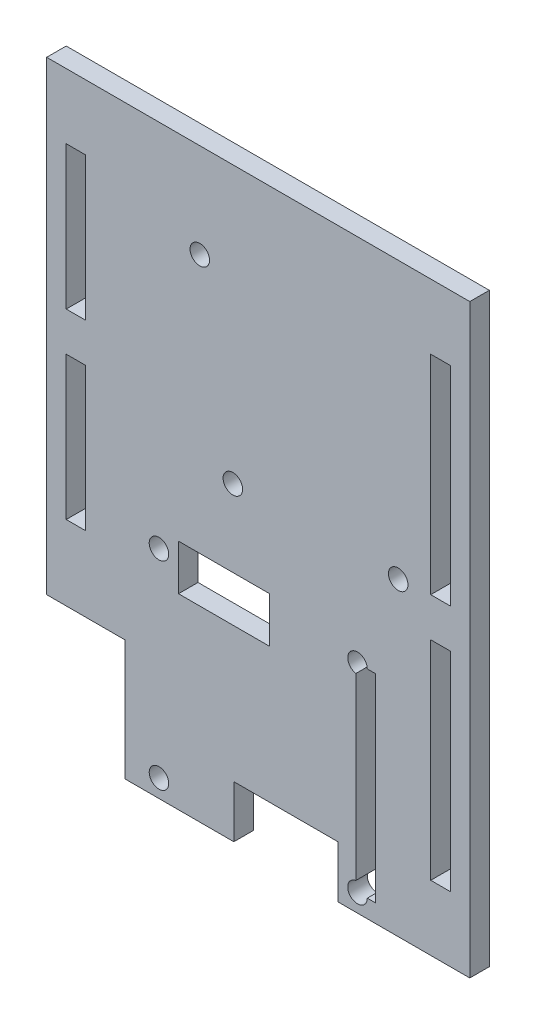
SolidWorks part; units mm, degrees
material "Custom Plastic"
ref_plane "Front Plane" through (0, 0, 0) normal (0, 0, 1) x (1, 0, 0)
ref_plane "Top Plane" through (0, 0, 0) normal (0, 1, 0) x (1, 0, 0)
ref_plane "Right Plane" through (0, 0, 0) normal (1, 0, 0) x (0, 0, -1)
sketch "Sketch1" plane through (0, 0, 0) normal (0, 0, 1) x (1, 0, 0)
  line L1 (-32.5, 45) -> (32.5, 45)
  line L2 (-32.5, 45) -> (-32.5, -45)
  line L3 (-32.5, -45) -> (32.5, -45)
  line L4 (32.5, 45) -> (32.5, -45)
  line L5 (-32.5, 45) -> (32.5, -45) construction
  line L6 (-32.5, -45) -> (32.5, 45) construction
  point P0 (0, 0)
  dimension "D1" = 65
  dimension "D2" = 90
extrude "Boss-Extrude1" add sketch "Sketch1" against normal blind 3
sketch "Sketch3" plane through (0, 0, 0) normal (0, 0, 1) x (1, 0, 0)
  line L0 (32.5, -45) -> (32.5, 45) construction
  line L3 (21.5, 2.56) -> (-3.9, 2.56) construction
  line L4 (32.5, 45) -> (-32.5, 45) construction
  circle A0 centre (-8.98, 30.5) radius 1.5
  circle A1 centre (-3.9, 2.56) radius 1.5
  circle A2 centre (21.5, 2.56) radius 1.5
  dimension "D5" = 3
  dimension "D6" = 3
  dimension "D7" = 3
  dimension "D1" = 27.94
  dimension "D2" = 5.08
  dimension "D3" = 25.4
  dimension "D4" = 14.5
  dimension "D8" = 11
extrude "Cut-Extrude2" cut sketch "Sketch3" against normal blind 3
sketch "Sketch4" plane through (0, 0, 0) normal (0, 0, 1) x (1, 0, 0)
  line L0 (-15.25, -11.75) -> (-15.25, -42.25) construction
  line L1 (-15.25, -42.25) -> (15.25, -42.25) construction
  line L2 (15.25, -42.25) -> (15.25, -11.75) construction
  circle A0 centre (-15.25, -42.25) radius 1.5
  circle A1 centre (-15.25, -11.75) radius 1.5
  circle A2 centre (15.25, -42.25) radius 1.5
  circle A3 centre (15.25, -11.75) radius 1.5
  dimension "D3" = 3
  dimension "D1" = 30.5
  dimension "D2" = 30.5
extrude "Cut-Extrude3" cut sketch "Sketch4" against normal through all
sketch "Sketch5" plane through (0, 0, 0) normal (0, 0, 1) x (1, 0, 0)
  line L0 (32.5, 45) -> (-32.5, 45) construction
  line L1 (29.5, -35) -> (26.5, -35)
  line L2 (29.5, -35) -> (29.5, -3)
  line L3 (29.5, -3) -> (26.5, -3)
  line L4 (26.5, -35) -> (26.5, -3)
  line L5 (29.5, 3) -> (26.5, 3)
  line L6 (29.5, 3) -> (29.5, 35)
  line L7 (29.5, 35) -> (26.5, 35)
  line L8 (26.5, 3) -> (26.5, 35)
  line L10 (32.5, -45) -> (32.5, 45) construction
  dimension "D1" = 6
  dimension "D2" = 32
  dimension "D3" = 10
  dimension "D4" = 3
  dimension "D5" = 3
extrude "Cut-Extrude4" cut sketch "Sketch5" against normal through all
sketch "Sketch6" plane through (0, 0, 0) normal (0, 0, 1) x (1, 0, 0)
  line L0 (-32.5, 45) -> (-32.5, -45) construction
  line L1 (-26.5, -15) -> (-29.5, -15)
  line L2 (-26.5, -15) -> (-26.5, 7)
  line L3 (-26.5, 7) -> (-29.5, 7)
  line L4 (-29.5, -15) -> (-29.5, 7)
  line L5 (-26.5, 13) -> (-29.5, 13)
  line L6 (-26.5, 13) -> (-26.5, 35)
  line L7 (-26.5, 35) -> (-29.5, 35)
  line L8 (-29.5, 13) -> (-29.5, 35)
  line L9 (-32.5, -45) -> (32.5, -45) construction
  line L10 (32.5, 45) -> (-32.5, 45) construction
  dimension "D1" = 3
  dimension "D2" = 3
  dimension "D3" = 30
  dimension "D4" = 6
  dimension "D5" = 10
extrude "Cut-Extrude5" cut sketch "Sketch6" against normal through all
sketch "Sketch7" plane through (0, 0, 0) normal (0, 0, 1) x (1, 0, 0)
  line L0 (16.75, -11.75) -> (13.75, -11.75) construction
  line L1 (18, -42.25) -> (15, -42.25)
  line L2 (18, -42.25) -> (18, -11.75)
  line L3 (18, -11.75) -> (15, -11.75)
  line L4 (15, -42.25) -> (15, -11.75)
  line L5 (16.75, -42.25) -> (13.75, -42.25) construction
  line L6 (-32.5, -45) -> (32.5, -45) construction
  line L7 (-12.25, -16.25) -> (1.75, -16.25)
  line L8 (-12.25, -16.25) -> (-12.25, -9.25)
  line L9 (-12.25, -9.25) -> (1.75, -9.25)
  line L10 (1.75, -16.25) -> (1.75, -9.25)
  line L11 (12.25, -45) -> (-3.75, -45)
  line L12 (12.25, -45) -> (12.25, -37)
  line L13 (12.25, -37) -> (-3.75, -37)
  line L14 (-3.75, -45) -> (-3.75, -37)
  circle A0 centre (15.25, -11.75) radius 1.5 construction
  circle A1 centre (15.25, -42.25) radius 1.5 construction
  circle A2 centre (-15.25, -11.75) radius 1.5 construction
  point P17 (15.25, -42.25)
  dimension "D1" = 2.5
  dimension "D2" = 3
  dimension "D3" = 7
  dimension "D4" = 14
  dimension "D5" = 3
  dimension "D6" = 3
  dimension "D7" = 2.75
  dimension "D8" = 8
  dimension "D9" = 16
extrude "Cut-Extrude6" cut sketch "Sketch7" against normal through all
sketch "Sketch8" plane through (0, 0, 0) normal (0, 0, 1) x (1, 0, 0)
  line L0 (-32.5, -45) -> (-3.75, -45) construction
  line L1 (-20.5, -45) -> (-32.5, -45)
  line L2 (-20.5, -45) -> (-20.5, -26.5)
  line L3 (-20.5, -26.5) -> (-32.5, -26.5)
  line L4 (-32.5, -45) -> (-32.5, -26.5)
  line L5 (-32.5, 45) -> (-32.5, -45) construction
  dimension "D1" = 12
  dimension "D2" = 18.5
extrude "Cut-Extrude7" cut sketch "Sketch8" against normal through all
